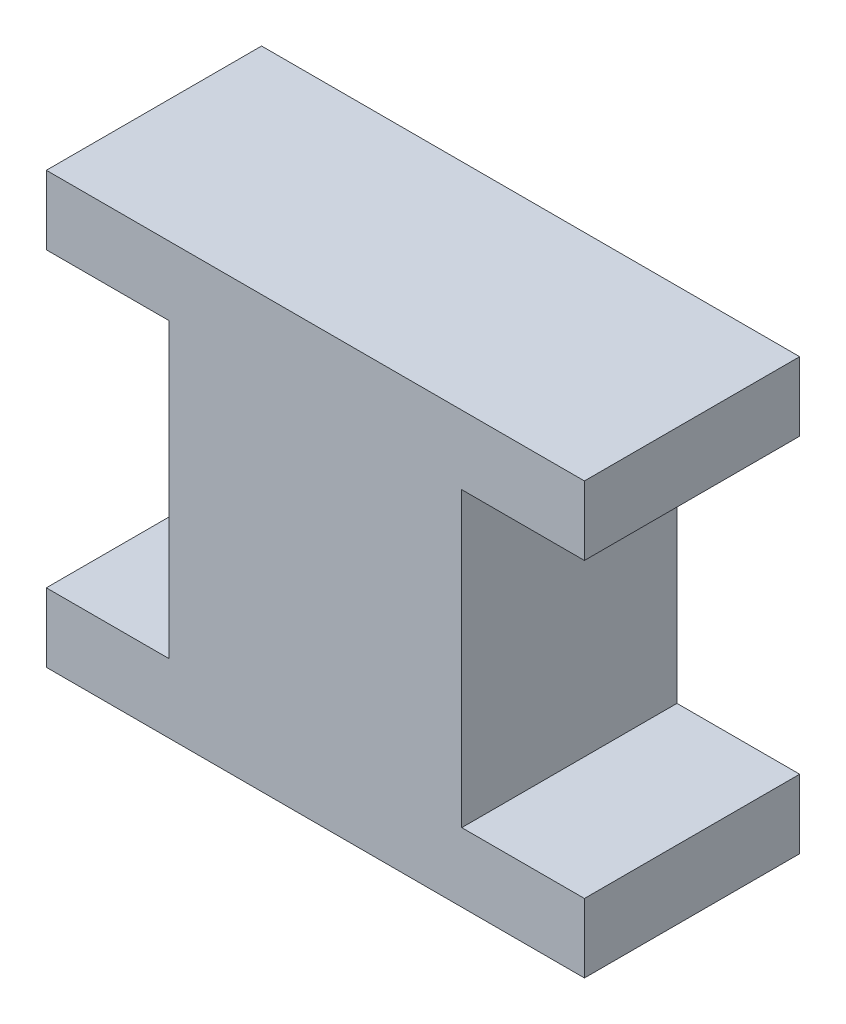
SolidWorks part; units mm, degrees
ref_plane "Front Plane" through (0, 0, 0) normal (0, 0, 1) x (1, 0, 0)
ref_plane "Top Plane" through (0, 0, 0) normal (0, 1, 0) x (1, 0, 0)
ref_plane "Right Plane" through (0, 0, 0) normal (1, 0, 0) x (0, 0, -1)
sketch "Sketch1" plane through (0, 0, 0) normal (0, 0, 1) x (1, 0, 0)
  line L0 (-3.4544, 3.4544) -> (-3.4544, -3.4544)
  line L1 (6.35, -5.08) -> (-6.35, -5.08)
  line L2 (6.35, -3.4544) -> (3.4544, -3.4544)
  line L3 (6.35, 5.08) -> (-6.35, 5.08)
  line L7 (-5.08, 5.08) -> (5.08, 5.08)
  line L8 (-3.4544, 3.4544) -> (-6.35, 3.4544)
  line L9 (-5.08, -5.08) -> (5.08, -5.08)
  line L10 (3.4544, 3.4544) -> (3.4544, -3.4544)
  line L13 (-6.35, 3.4544) -> (-6.35, 5.08)
  line L14 (-3.4544, -3.4544) -> (-6.35, -3.4544)
  line L15 (-6.35, -3.4544) -> (-6.35, -5.08)
  line L16 (6.35, -3.4544) -> (6.35, -5.08)
  line L17 (6.35, 3.4544) -> (6.35, 5.08)
  line L18 (6.35, 3.4544) -> (3.4544, 3.4544)
  point P0 (0, 0)
  point P6 (0, 0)
  point P14 (-3.4544, 0)
  dimension "D1" = 12.7
  dimension "D2" = 10.16
  dimension "D3" = 10.16
  dimension "D4" = 10.16
  dimension "D5" = 6.9088
  dimension "D6" = 1.6256
  dimension "D7" = 6.9088
  dimension "D8" = 1.6256
  dimension "D9" = 2.8956
  dimension "D10" = 2.8956
  dimension "D11" = 6.9088
extrude "Boss-Extrude1" add sketch "Sketch1" along normal blind 5.08 contours L3 L13 L8 L0 L14 L15 L1 L16 L2 L10 L18 L17
